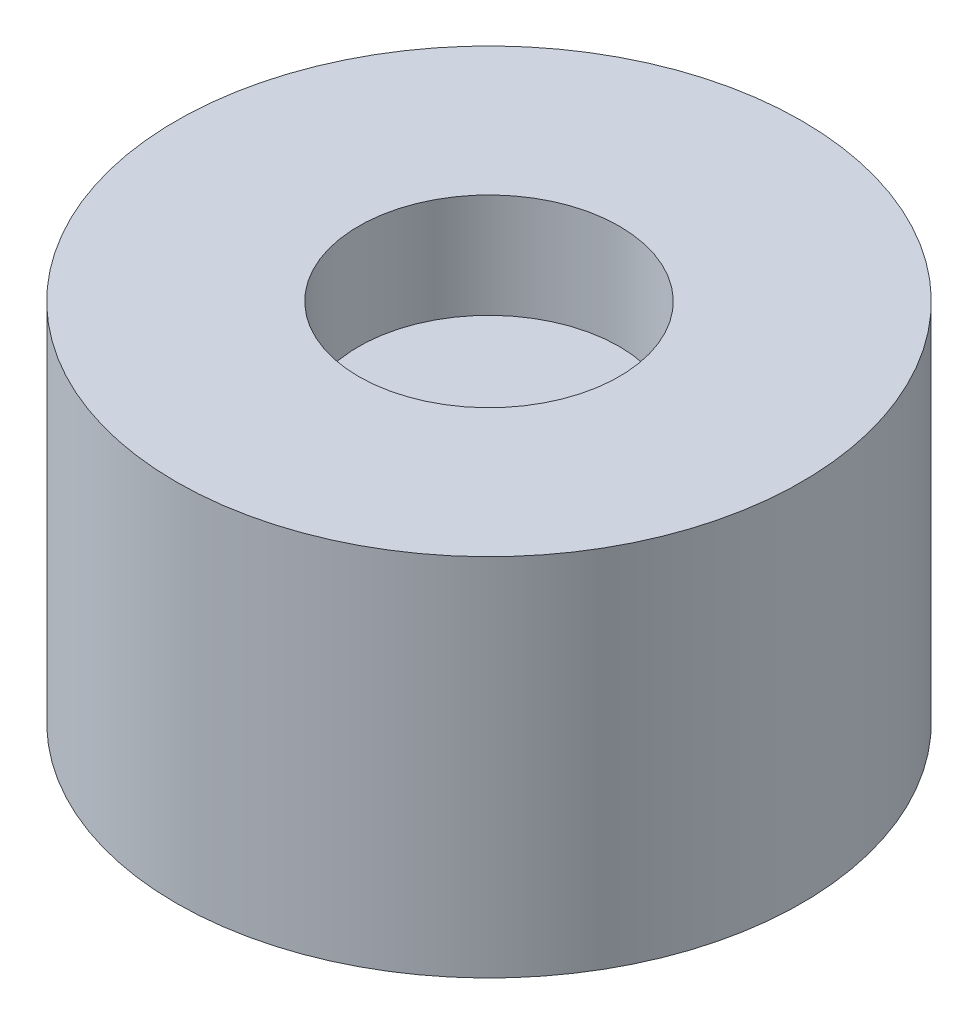
SolidWorks part; units mm, degrees
ref_plane "Front Plane" through (0, 0, 0) normal (0, 0, 1) x (1, 0, 0)
ref_plane "Top Plane" through (0, 0, 0) normal (0, 1, 0) x (1, 0, 0)
ref_plane "Right Plane" through (0, 0, 0) normal (1, 0, 0) x (0, 0, -1)
sketch "Sketch1" plane through (0, 0, 0) normal (0, 1, 0) x (1, 0, 0)
  circle A0 centre (0, 0) radius 6
  dimension "D1" = 12
extrude "Boss-Extrude1" add sketch "Sketch1" along normal blind 7
sketch "Sketch2" plane through (0, 7, 0) normal (0, 1, 0) x (1, 0, 0)
  circle A0 centre (0, 0) radius 2.5
  dimension "D1" = 5
extrude "Cut-Extrude1" cut sketch "Sketch2" against normal blind 2
sketch "Sketch4" plane through (0, 0, 0) normal (0, -1, 0) x (1, 0, 0)
  circle A0 centre (0, 0) radius 1
  dimension "D1" = 2
extrude "Cut-Extrude3" cut sketch "Sketch4" against normal blind 2
fillet "Fillet1" radius 1 1 edges at (0, 2, -1)
